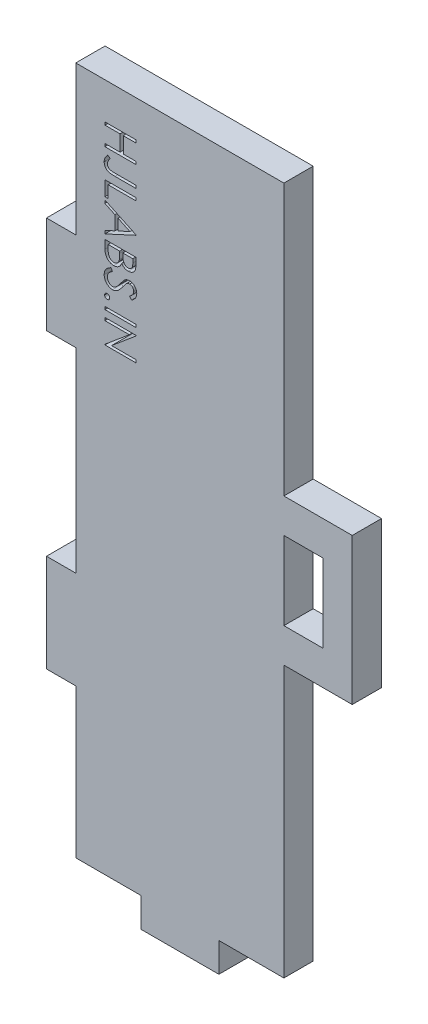
SolidWorks part; units mm, degrees
ref_plane "Front Plane" through (0, 0, 0) normal (0, 0, 1) x (1, 0, 0)
ref_plane "Top Plane" through (0, 0, 0) normal (0, 1, 0) x (1, 0, 0)
ref_plane "Right Plane" through (0, 0, 0) normal (1, 0, 0) x (0, 0, -1)
sketch "Sketch1" plane through (0, 0, 0) normal (0, 0, 1) x (1, 0, 0)
  line L5 (3, -29) -> (-24.3118, 47.5) construction
  line L6 (3, 47.5) -> (-24.3118, -29) construction
  line L7 (3, -10.75) -> (0, -10.75) construction
  line L10 (3, -0.75) -> (0, -0.75) construction
  line L12 (3, 19.25) -> (0, 19.25) construction
  line L13 (3, 29.25) -> (0, 29.25) construction
  line L25 (-10.6559, -35.4999) -> (-10.6559, 53.9999) construction
  line L27 (-24.3118, 19.25) -> (-21.3118, 19.25)
  line L28 (-24.3118, 29.25) -> (-21.3118, 29.25)
  line L29 (-24.3118, -0.75) -> (-21.3118, -0.75)
  line L30 (-24.3118, -10.75) -> (-21.3118, -10.75)
  line L31 (-24.3118, -10.75) -> (-24.3118, -0.75)
  line L32 (-21.3118, -10.75) -> (-21.3118, -26)
  line L33 (-21.3118, -0.75) -> (-21.3118, 19.25)
  line L34 (-21.3118, 29.25) -> (-21.3118, 44.5)
  line L35 (-24.3118, 19.25) -> (-24.3118, 29.25)
  line L43 (-2, 44.5) -> (0, 44.5) construction
  line L44 (-19.3118, 44.5) -> (-2, 44.5) construction
  line L45 (-21.3118, 44.5) -> (-19.3118, 44.5) construction
  line L47 (0, -26) -> (0, 1.75)
  line L48 (-21.3118, 9.25) -> (16.8002, 9.25) construction
  line L49 (-2, 44.5) -> (0, 44.5)
  line L50 (-19.3118, 44.5) -> (-2, 44.5)
  line L51 (-21.3118, 44.5) -> (-19.3118, 44.5)
  line L52 (0, -26) -> (-2, -26)
  line L53 (-19.3118, -26) -> (-21.3118, -26)
  line L54 (-19.3118, -26) -> (-2, -26)
  line L55 (0, 16.75) -> (0, 44.5)
  line L56 (0, 1.75) -> (7, 1.75)
  line L58 (0, 16.75) -> (7, 16.75)
  line L59 (7, 1.75) -> (7, 16.75)
  line L60 (0, 1.75) -> (7, 16.75) construction
  line L61 (0, 16.75) -> (7, 1.75) construction
  line L62 (0, 16.75) -> (0, 1.75) construction
  line L64 (0, 5.25) -> (4, 5.25)
  line L65 (0, 5.25) -> (0, 13.25)
  line L66 (0, 13.25) -> (4, 13.25)
  line L67 (4, 5.25) -> (4, 13.25)
  line L68 (0, 5.25) -> (4, 13.25) construction
  line L69 (0, 13.25) -> (4, 5.25) construction
  point P4 (-10.6559, 9.25)
  point P18 (-10.6559, 9.25)
  point P32 (3.5, 9.25)
  point P41 (2, 9.25)
  point P46 (0, 0)
  point P47 (3, -29)
  dimension "D1" = 7
  dimension "D2" = 15
  dimension "D3" = 4
  dimension "D4" = 8
extrude "Boss-Extrude1" add sketch "Sketch1" along normal blind 3
sketch "Sketch6" plane through (0, 0, 3) normal (0, 0, 1) x (1, 0, 0)
  line L0 (-18.3216, 41.1695) -> (-18.3216, -20.0325) construction
  text T0 "HJLABS.IN"
extrude "Cut-Extrude2" cut sketch "Sketch6" against normal blind 3
sketch "Sketch7" plane through (0, 0, 3) normal (0, 0, 1) x (1, 0, 0)
  line L0 (-14.6559, -26) -> (-14.6559, -29) construction
  line L1 (-6.6559, -26) -> (-6.6559, -29) construction
  line L2 (-14.6559, -26) -> (-14.6559, -29)
  line L3 (-6.6559, -26) -> (-6.6559, -29)
  line L4 (-6.6559, -26) -> (-14.6559, -26)
  line L5 (-6.6559, -29) -> (-14.6559, -29)
extrude "Boss-Extrude2" add sketch "Sketch7" against normal blind 3
